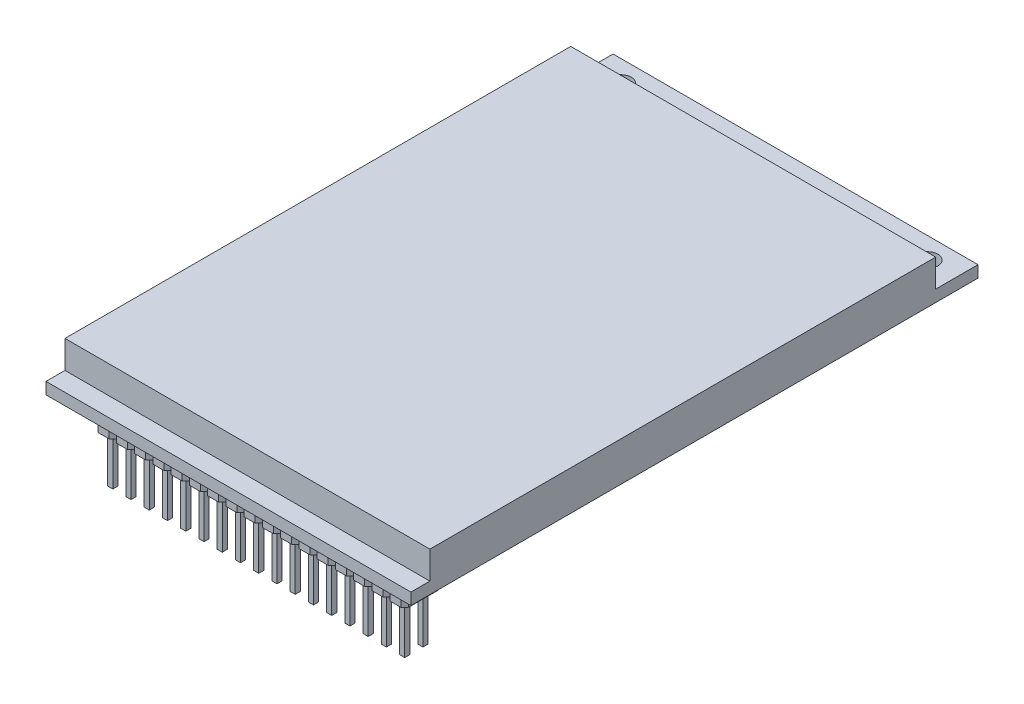
SolidWorks part; units mm, degrees
ref_plane "前视基准面" through (0, 0, 0) normal (0, 0, 1) x (1, 0, 0)
ref_plane "上视基准面" through (0, 0, 0) normal (0, 1, 0) x (1, 0, 0)
ref_plane "右视基准面" through (0, 0, 0) normal (1, 0, 0) x (0, 0, -1)
sketch "草图1" plane through (0, 0, 0) normal (0, 1, 0) x (1, 0, 0)
  line L0 (0, 0) -> (0, 57.7083) construction
  line L1 (25, -38.85) -> (-25, -38.85)
  line L2 (25, -38.85) -> (25, 38.85)
  line L3 (25, 38.85) -> (-25, 38.85)
  line L4 (-25, -38.85) -> (-25, 38.85)
  line L5 (25, -38.85) -> (-25, 38.85) construction
  line L6 (25, 38.85) -> (-25, -38.85) construction
  circle A0 centre (-21, 35.95) radius 1.4
  circle A1 centre (21, 35.95) radius 1.4
  point P0 (0, 0)
  dimension "D3" = 2.8
  dimension "D4" = 2.9
  dimension "D1" = 50
  dimension "D2" = 77.7
  dimension "D5" = 42
extrude "凸台-拉伸1" add sketch "草图1" along normal blind 1.6
sketch "草图2" plane through (0, 1.6, 0) normal (0, 1, 0) x (1, 0, 0)
  line L0 (-25, 38.85) -> (-25, -38.85) construction
  line L1 (-25, 33.05) -> (25, 33.05)
  line L2 (-25, 33.05) -> (-25, -36.25)
  line L3 (-25, -36.25) -> (25, -36.25)
  line L4 (25, 33.05) -> (25, -36.25)
  line L5 (25, -38.85) -> (25, 38.85) construction
  line L6 (-25, -38.85) -> (25, -38.85) construction
  dimension "D1" = 69.3
  dimension "D2" = 2.6
extrude "凸台-拉伸2" add sketch "草图2" along normal blind 3.8
sketch "草图3" plane through (0, 0, 0) normal (0, -1, 0) x (1, 0, 0)
  line L0 (1.25, 31.45) -> (0.75, 30.95)
  line L1 (0.75, 35.95) -> (-0.75, 35.95)
  line L2 (1.25, 35.45) -> (1.25, 31.45)
  line L3 (0.75, 30.95) -> (-0.75, 30.95)
  line L4 (-1.25, 35.45) -> (-1.25, 31.45)
  line L5 (1.25, 35.95) -> (-1.25, 30.95) construction
  line L6 (1.25, 30.95) -> (-1.25, 35.95) construction
  line L7 (-1.25, 31.45) -> (-0.75, 30.95)
  line L8 (0.75, 35.95) -> (1.25, 35.45)
  line L9 (-0.75, 35.95) -> (-1.25, 35.45)
  line L10 (-25, 38.85) -> (25, 38.85) construction
  point P0 (0, 33.45)
  dimension "D1" = 5
  dimension "D2" = 2.5
  dimension "D3" = 2.9
extrude "凸台-拉伸3" add sketch "草图3" along normal blind 3.8
sketch "草图4" plane through (0, -3.8, 0) normal (0, -1, 0) x (1, 0, 0)
  line L0 (0.75, 30.95) -> (-0.75, 35.95) construction
  line L1 (0.35, 32.55) -> (-0.35, 32.55)
  line L2 (0.35, 32.55) -> (0.35, 31.85)
  line L3 (0.35, 31.85) -> (-0.35, 31.85)
  line L4 (-0.35, 32.55) -> (-0.35, 31.85)
  line L5 (0.35, 32.55) -> (-0.35, 31.85) construction
  line L6 (0.35, 31.85) -> (-0.35, 32.55) construction
  line L7 (0.75, 35.95) -> (-0.75, 30.95) construction
  line L8 (0.75, 35.95) -> (-0.75, 35.95) construction
  line L9 (0, 33.45) -> (-2.9025, 33.45) construction
  line L10 (0.35, 35.05) -> (-0.35, 34.35) construction
  line L11 (0.35, 34.35) -> (-0.35, 35.05) construction
  line L12 (-0.35, 34.35) -> (-0.35, 35.05)
  line L13 (0.35, 35.05) -> (-0.35, 35.05)
  line L14 (0.35, 34.35) -> (0.35, 35.05)
  line L15 (0.35, 34.35) -> (-0.35, 34.35)
  point P0 (0, 32.2)
  point P18 (0, 33.45)
  point P22 (0, 34.7)
  dimension "D1" = 0.7
  dimension "D2" = 2.5
extrude "凸台-拉伸4" add sketch "草图4" along normal blind 6.6
pattern_linear "阵列(线性)2" count 9 spacing 2.5 along (1, 0, 0) count 9 spacing 2.5 along (-1, 0, 0) of "凸台-拉伸3", "凸台-拉伸4"
